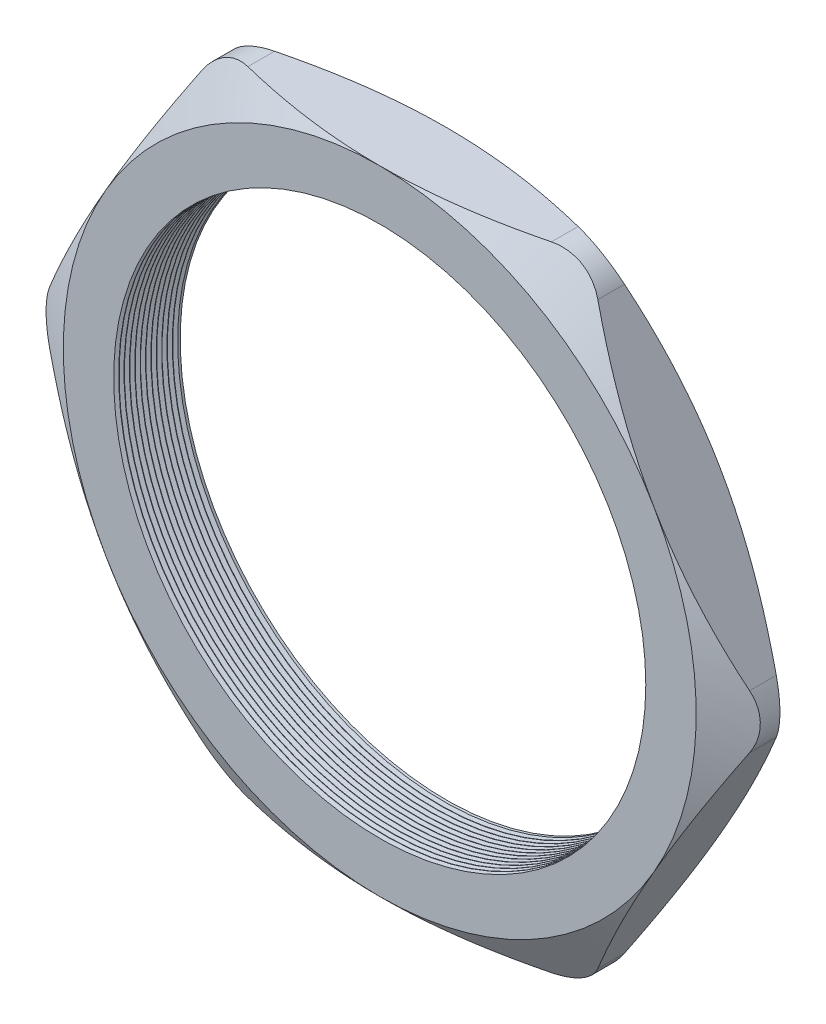
SolidWorks part; units mm, degrees
ref_plane "Front Plane" through (0, 0, 0) normal (0, 0, 1) x (1, 0, 0)
ref_plane "Top Plane" through (0, 0, 0) normal (0, 1, 0) x (1, 0, 0)
ref_plane "Right Plane" through (0, 0, 0) normal (1, 0, 0) x (0, 0, -1)
sketch "Sketch1" plane through (0, 0, 0) normal (0, 0, 1) x (1, 0, 0)
  line L1 (-43.2609, 0) -> (-21.6304, -37.465)
  line L2 (-21.6304, -37.465) -> (21.6304, -37.465)
  line L3 (21.6304, -37.465) -> (43.2609, 0)
  line L4 (43.2609, 0) -> (21.6304, 37.465)
  line L5 (21.6304, 37.465) -> (-21.6304, 37.465)
  line L6 (-21.6304, 37.465) -> (-43.2609, 0)
  circle A0 centre (0, 0) radius 37.465 construction
  circle A1 centre (0, 0) radius 31.496
  dimension "TS" = 62.992
  dimension "H" = 74.93
extrude "Extrude1" add sketch "Sketch1" along normal blind 7.874
sketch "Sketch2" plane through (0, 0, 7.874) normal (0, 0, 1) x (1, 0, 0)
  line L0 (21.6304, 37.465) -> (-21.6304, 37.465) construction
  circle A0 centre (0, 0) radius 37.465
extrude "Cut-Extrude1" cut sketch "Sketch2" against normal through all draft 60 flip side to cut
sketch "Sketch3" plane through (0, 0, 0) normal (0, 0, -1) x (-1, 0, 0)
  line L0 (-21.6304, 37.465) -> (21.6304, 37.465) construction
  circle A0 centre (0, 0) radius 37.465
extrude "Cut-Extrude2" cut sketch "Sketch3" against normal through all draft 60 flip side to cut
fillet "Fillet1" radius 6.35 6 edges at (43.2609, 0, 3.937) (21.6304, -37.465, 3.937) (-21.6304, -37.465, 3.937) (-43.2609, 0, 3.937) (-21.6304, 37.465, 3.937) (21.6304, 37.465, 3.937)
sketch "Sketch4" plane through (0, 0, 0) normal (0, 1, 0) x (1, 0, 0)
  line L0 (-31.496, -7.874) -> (-31.496, -7.2874)
  line L1 (-31.496, 0) -> (-31.496, -7.874) construction
  line L2 (-31.496, -7.2874) -> (-32.004, -7.5807)
  line L3 (-32.004, -7.5807) -> (-31.496, -7.874)
  dimension "D1" = 60
  dimension "D2" = 60
  dimension "D3" = 0.508
revolve "Cut-Revolve1" cut sketch "Sketch4" angle 360 about axis through (0, 0, 0) along (0, 0, 1)
pattern_linear "LPattern1" count 12 spacing 0.635 along (0, 0, -1) of "Cut-Revolve1"
